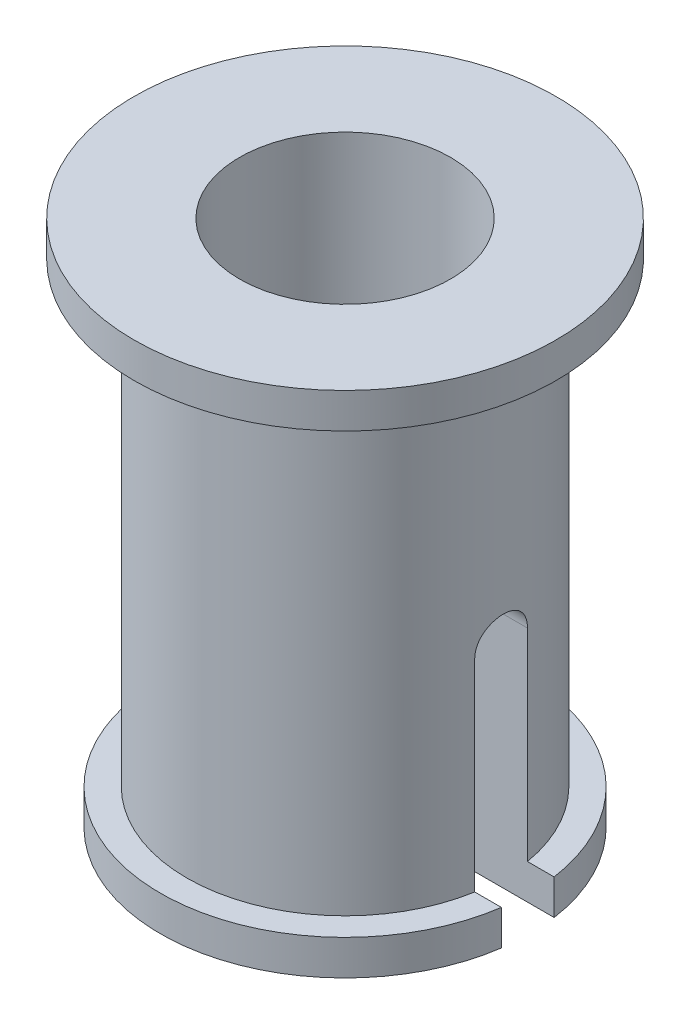
SolidWorks part; units mm, degrees
ref_plane "Front Plane" through (0, 0, 0) normal (0, 0, 1) x (1, 0, 0)
ref_plane "Top Plane" through (0, 0, 0) normal (0, 1, 0) x (1, 0, 0)
ref_plane "Right Plane" through (0, 0, 0) normal (1, 0, 0) x (0, 0, -1)
sketch "Sketch1" plane through (0, 0, 0) normal (0, 1, 0) x (1, 0, 0)
  circle A0 centre (0, 0) radius 1
  circle A1 centre (0, 0) radius 1.5
  point P5 (0, 0)
  dimension "D1" = 3
  dimension "D2" = 2
extrude "Boss-Extrude1" add sketch "Sketch1" along normal blind 5
sketch "Sketch2" plane through (0, 5, 0) normal (0, 1, 0) x (1, 0, 0)
  circle A0 centre (0, 0) radius 1
  circle A1 centre (0, 0) radius 2
  dimension "D1" = 4
extrude "Boss-Extrude2" add sketch "Sketch2" against normal blind 0.3333
sketch "Sketch3" plane through (0, 0, 0) normal (0, -1, 0) x (-1, 0, 0)
  circle A0 centre (0, 0) radius 1.75
  circle A1 centre (0, 0) radius 1
  dimension "D1" = 3.5
extrude "Boss-Extrude4" add sketch "Sketch3" against normal blind 0.3333
sketch "Sketch4" plane through (0, 0, 0) normal (1, 0, 0) x (0, 0, -1)
  line L1 (0.25, 0) -> (-0.25, 0)
  line L2 (0.25, 0) -> (0.25, 2.25)
  line L3 (0.25, 2.25) -> (-0.25, 2.25)
  line L4 (-0.25, 0) -> (-0.25, 2.25)
  circle A0 centre (0, 2.25) radius 0.25
  point P7 (0, 0)
  dimension "D1" = 0.5
  dimension "D2" = 2.25
extrude "Cut-Extrude1" cut sketch "Sketch4" against normal through all both and the other way through all contours L3 A0
